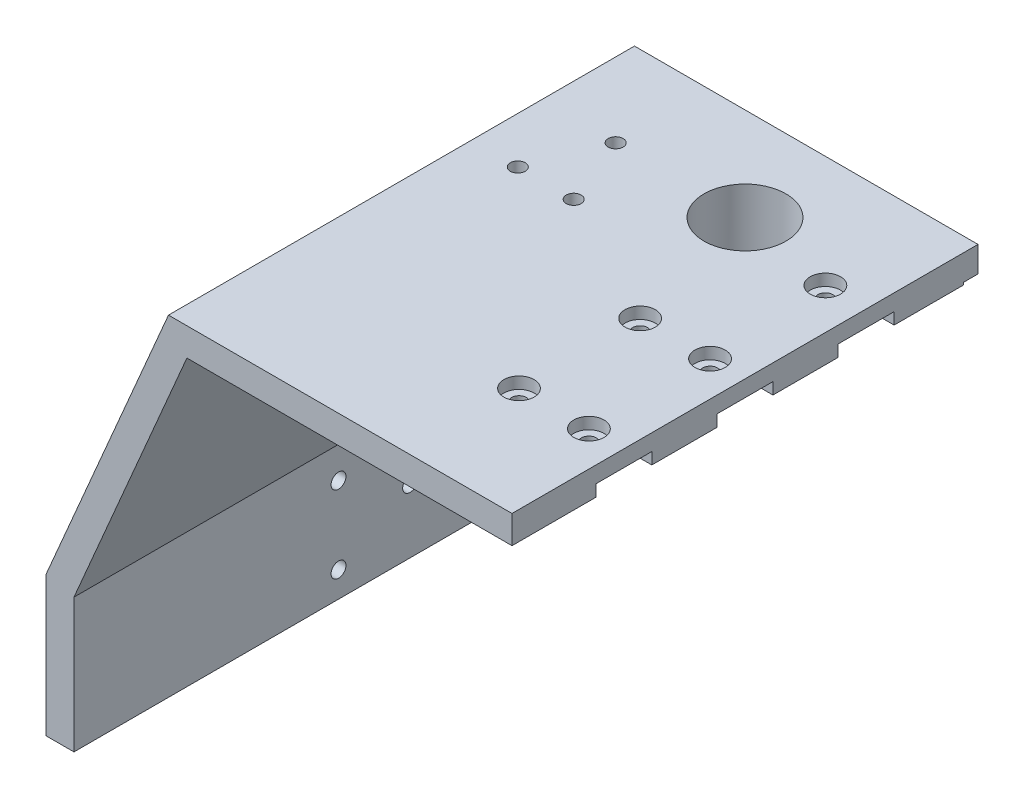
SolidWorks part; units mm, degrees
ref_plane "Alzado" through (0, 0, 0) normal (0, 0, 1) x (1, 0, 0)
ref_plane "Planta" through (0, 0, 0) normal (0, 1, 0) x (1, 0, 0)
ref_plane "Vista lateral" through (0, 0, 0) normal (1, 0, 0) x (0, 0, -1)
sketch "Croquis1" plane through (0, 0, 0) normal (0, 0, 1) x (1, 0, 0)
  line L1 (-100, 25) -> (-73.7179, 86.3249) construction
  line L2 (-73.7179, 86.3249) -> (73.7179, 86.3249) construction
  line L3 (100, 25) -> (100, -5) construction
  line L4 (100, 25) -> (73.7179, 86.3249) construction
  line L5 (-100, 25) -> (-100, -5)
  line L6 (-100, 25) -> (-73.7179, 86.3249)
  line L7 (-73.7179, 86.3249) -> (73.7179, 86.3249)
  line L8 (100, 25) -> (100, -5)
  line L9 (100, 25) -> (73.7179, 86.3249)
  line L10 (-94, 23.7685) -> (-94, -5)
  line L11 (-94, 23.7685) -> (-69.7615, 80.3249)
  line L12 (-69.7615, 80.3249) -> (69.7615, 80.3249)
  line L13 (94, 23.7685) -> (69.7615, 80.3249)
  line L14 (94, 23.7685) -> (94, -5)
  line L15 (-94, -5) -> (-100, -5)
  line L16 (100, -5) -> (94, -5)
  dimension "D2" = 30
  dimension "D1" = 6
extrude "Saliente-Extruir1" add sketch "Croquis1" along normal blind 100
sketch "Croquis3" plane through (0, 86.3249, 0) normal (0, 1, 0) x (1, 0, 0)
  line L0 (73.7179, 0) -> (-73.7179, 0) construction
  line L1 (73.7179, -100) -> (73.7179, 0) construction
  line L2 (-73.7179, -100) -> (-73.7179, 0) construction
  circle A2 centre (-30, -20) radius 8.8
  circle A3 centre (30, -20) radius 8.8
  dimension "D4" = 17.6
  dimension "D5" = 17.6
  dimension "D1" = 20
  dimension "D2" = 20
  dimension "D3" = 43.7179
  dimension "D6" = 43.7179
extrude "Cortar-Extruir1" cut sketch "Croquis3" against normal up to next
ref_plane "Plano1" through (-87.4795, 68.8361, 0) normal (-0.7859, 0.6184, 0) x (0, 0, -1)
sketch "Croquis4" plane through (-87.4795, 68.8361, 0) normal (-0.7859, 0.6184, 0) x (0, 0, -1)
  line L0 (0, -22.254) -> (0, 42.1921) construction
  line L1 (-100, -22.254) -> (0, -22.254) construction
  line L2 (-100, -22.254) -> (-100, 42.1921) construction
  line L3 (-100, 42.1921) -> (0, 42.1921) construction
  line L4 (0, -22.254) -> (0, 42.1921) construction
  line L5 (-100, -22.254) -> (0, -22.254) construction
  line L6 (-100, -22.254) -> (-100, 42.1921) construction
  line L7 (-100, 42.1921) -> (0, 42.1921) construction
  line L8 (0, 9.9691) -> (-100, 9.9691) construction
  circle A0 centre (-20, 9.9691) radius 8.8
  dimension "D1" = 17.6
  dimension "D2" = 20
extrude "Cortar-Extruir2" cut sketch "Croquis4" against normal up to next
mirror "Simetría1" about plane through (0, 0, 0) normal (1, 0, 0) of "Cortar-Extruir2"
sketch "Croquis5" plane through (0, 80.3249, 0) normal (0, -1, 0) x (1, 0, 0)
  line L0 (15.175, 0) -> (15.175, 2.3)
  line L1 (15.175, 2.3) -> (3.7842, 2.3)
  line L3 (-3.7842, 2.3) -> (-15.175, 2.3)
  line L4 (-15.175, 2.3) -> (-15.175, 0)
  line L10 (-14.875, 0) -> (-3.2619, 0)
  line L11 (3.2619, 0) -> (14.875, 0)
  line L12 (14.875, 0) -> (14.875, 2)
  line L13 (14.875, 2) -> (3.7202, 2)
  line L14 (-3.7202, 2) -> (-14.875, 2)
  line L15 (-14.875, 2) -> (-14.875, 0)
  line L17 (-15.175, 0) -> (3.2619, 0)
  line L19 (-3.2619, 0) -> (15.175, 0)
  line L20 (14.875, 0) -> (14.875, 2)
  line L22 (14.875, 2) -> (3.7202, 2)
  line L23 (-3.7202, 2) -> (-14.875, 2)
  line L24 (-14.875, 2) -> (-14.875, 0)
  arc A0 (3.7842, 2.3) -> (-3.7842, 2.3) centre (0, -6.25) ccw
  arc A3 (3.2619, 0) -> (-3.2619, 0) centre (0, -6.25) ccw
  arc A4 (3.7202, 2) -> (-3.7202, 2) centre (0, -6.25) ccw
  arc A5 (3.2619, 0) -> (-3.2619, 0) centre (0, -6.25) ccw
  arc A7 (3.7202, 2) -> (-3.7202, 2) centre (0, -6.25) ccw
  dimension "D1" = 0
  dimension "D2" = 0.3
extrude "Cortar-Extruir3" cut sketch "Croquis5" against normal blind 0.5
sketch "Croquis6" plane through (-100, 0, 0) normal (-1, 0, 0) x (0, 0, 1)
  circle A0 centre (43.227, 0.4977) radius 1.6 construction
  circle A1 centre (27.8635, 8.7685) radius 1.6 construction
  circle A2 centre (43.227, 17.0392) radius 1.6 construction
  circle A3 centre (43.227, 0.4977) radius 1.6
  circle A4 centre (27.8635, 8.7685) radius 1.6
  circle A5 centre (43.227, 17.0392) radius 1.6
extrude "Cortar-Extruir4" cut sketch "Croquis6" against normal up to next
sketch "Croquis7" plane through (-100, 0, 0) normal (-1, 0, 0) x (0, 0, 1)
  circle A0 centre (27.8635, 8.7685) radius 3.25
  circle A1 centre (43.227, 0.4977) radius 3.25
  circle A2 centre (43.227, 17.0392) radius 3.25
  dimension "D1" = 6.5
extrude "Cortar-Extruir5" cut sketch "Croquis7" against normal blind 2.5
mirror "Simetría2" about plane through (0, 0, 0) normal (1, 0, 0) of "Cortar-Extruir5", "Cortar-Extruir4"
sketch "Croquis8" plane through (0, 80.3249, 0) normal (0, -1, 0) x (1, 0, 0)
  line L0 (0, 100) -> (0, 0) construction
  line L1 (-37.5, 82) -> (37.5, 82)
  line L3 (-37.5, 70) -> (37.5, 70)
  line L5 (-69.7615, 100) -> (69.7615, 100) construction
  line L7 (-37.5, 56) -> (37.5, 56)
  line L8 (-37.5, 56) -> (-37.5, 44)
  line L9 (-37.5, 44) -> (37.5, 44)
  line L10 (37.5, 56) -> (37.5, 44)
  line L11 (-69.7615, 50) -> (69.7615, 50) construction
  line L12 (-69.7615, 100) -> (-69.7615, 0) construction
  line L13 (69.7615, 100) -> (69.7615, 0) construction
  line L14 (-17.5, 30) -> (17.5, 30)
  line L15 (-17.5, 30) -> (-17.5, 18)
  line L16 (-17.5, 18) -> (17.5, 18)
  line L17 (17.5, 30) -> (17.5, 18)
  line L19 (-73.7179, 0) -> (73.7179, 0) construction
  line L20 (-37.5, 76) -> (37.5, 76) construction
  line L21 (-37.5, 70) -> (-37.5, 82)
  line L24 (37.5, 82) -> (37.5, 70)
  point P29 (37.5, 76)
  dimension "D1" = 12
  dimension "D3" = 12
  dimension "D4" = 30
  dimension "D5" = 75
  dimension "D6" = 12
  dimension "D7" = 30
  dimension "D8" = 35
  dimension "D9" = 75
extrude "Cortar-Extruir6" cut sketch "Croquis8" against normal blind 2.5
sketch "Croquis9" plane through (0, 82.8249, 0) normal (0, -1, 0) x (1, 0, 0)
  line L0 (-37.4, 76) -> (37.4, 76) construction
  line L1 (-37.5, 50) -> (37.5, 50) construction
  line L2 (-37.5, 56) -> (-37.5, 44) construction
  line L3 (-37.4, 81.9) -> (-37.4, 70.1) construction
  line L4 (37.5, 44) -> (37.5, 56) construction
  line L5 (-17.5, 24) -> (17.5, 24) construction
  line L6 (37.4, 70.1) -> (37.4, 81.9) construction
  line L7 (-37.5, 82) -> (-37.5, 70) construction
  line L8 (73.7179, 0) -> (-73.7179, 0)
  line L9 (73.7179, -6) -> (73.7179, 0)
  line L10 (-73.7179, -6) -> (73.7179, -6)
  line L11 (-73.7179, 0) -> (-73.7179, -6)
  line L12 (73.7179, 0) -> (-73.7179, 0) construction
  line L14 (0, 100) -> (0, 0) construction
  line L15 (-69.7615, 100) -> (69.7615, 100) construction
  line L23 (-17.5, 30) -> (-17.5, 18) construction
  line L24 (17.5, 18) -> (17.5, 30) construction
  line L25 (-37.5, 56) -> (-37.5, 44) construction
  line L28 (0, 18) -> (-17.5, 30) construction
  line L29 (-17.5, 18) -> (17.5, 18) construction
  line L30 (0, 30) -> (-17.5, 18) construction
  line L31 (17.5, 30) -> (-17.5, 30) construction
  circle A7 centre (-22.5, 76) radius 1.6
  circle A8 centre (-7.5, 76) radius 1.6
  circle A9 centre (7.5, 76) radius 1.6
  circle A10 centre (22.5, 76) radius 1.6
  circle A15 centre (-22.5, 50) radius 1.6
  circle A16 centre (-7.5, 50) radius 1.6
  circle A17 centre (7.5, 50) radius 1.6
  circle A18 centre (22.5, 50) radius 1.6
  circle A19 centre (-8.75, 24) radius 1.6
  circle A21 centre (8.75, 24) radius 1.6
  dimension "D1" = 3.2
  dimension "D2" = 15
  dimension "D3" = 15
  dimension "D4" = 15
  dimension "D7" = 15
  dimension "D11" = 3.2
  dimension "D13" = 3.2
  dimension "D5" = 15
  dimension "D6" = 0
  dimension "D8" = 15
  dimension "D10" = 15
  dimension "D9" = 15
extrude "Cortar-Extruir7" cut sketch "Croquis9" against normal up to next
sketch "Croquis10" plane through (0, 86.3249, 0) normal (0, 1, 0) x (1, 0, 0)
  circle A0 centre (-22.5, -50) radius 3.25
  circle A1 centre (-7.5, -50) radius 3.25
  circle A2 centre (7.5, -50) radius 3.25
  circle A3 centre (22.5, -50) radius 3.25
  circle A4 centre (8.75, -24) radius 3.25
  circle A5 centre (-8.75, -24) radius 3.25
  circle A6 centre (22.5, -50) radius 1.6 construction
  circle A7 centre (7.5, -50) radius 1.6 construction
  circle A8 centre (-7.5, -50) radius 1.6 construction
  circle A9 centre (-22.5, -50) radius 1.6 construction
  circle A10 centre (22.5, -76) radius 3.25
  circle A11 centre (7.5, -76) radius 3.25
  circle A12 centre (-7.5, -76) radius 3.25
  circle A13 centre (-22.5, -76) radius 3.25
  circle A14 centre (-8.75, -24) radius 1.6 construction
  circle A15 centre (8.75, -24) radius 1.6 construction
  dimension "D1" = 6.5
  dimension "D2" = 6.5
  dimension "D3" = 6.5
  dimension "D4" = 6.5
  dimension "D5" = 6.5
extrude "Cortar-Extruir8" cut sketch "Croquis10" against normal blind 2.5
sketch "Croquis11" plane through (0, 80.3249, 0) normal (0, -1, 0) x (1, 0, 0)
  circle A0 centre (30, 20) radius 8.8 construction
  circle A1 centre (-30, 20) radius 8.8 construction
  circle A2 centre (30, 20) radius 8.8
  circle A3 centre (-30, 20) radius 8.8
  circle A4 centre (-30, 20) radius 10.3
  circle A5 centre (30, 20) radius 10.3
  dimension "D1" = 1.5
extrude "Saliente-Extruir2" add sketch "Croquis11" along normal blind 10
ref_plane "Plano2" through (-63.9034, 50.2844, 0) normal (-0.7859, 0.6184, 0) x (0, 0, -1)
sketch "Croquis12" plane through (-63.9034, 50.2844, 0) normal (-0.7859, 0.6184, 0) x (0, 0, -1)
  circle A0 centre (-20, 9.9691) radius 8.8 construction
  circle A1 centre (-20, 9.9691) radius 8.8
  circle A2 centre (-20, 9.9691) radius 10.3
  dimension "D1" = 1.5
extrude "Saliente-Extruir3" add sketch "Croquis12" along normal up to next
sketch "Croquis13" plane through (0, 80.3249, 0) normal (0, -1, 0) x (1, 0, 0)
  circle A0 centre (57.7615, 20) radius 1.6 construction
  circle A1 centre (51.7615, 35) radius 1.6 construction
  circle A2 centre (63.7615, 35) radius 1.6 construction
  circle A3 centre (-57.7615, 20) radius 1.6 construction
  circle A4 centre (-63.7615, 35) radius 1.6 construction
  circle A5 centre (-51.7615, 35) radius 1.6 construction
  circle A6 centre (57.7615, 20) radius 1.6
  circle A7 centre (51.7615, 35) radius 1.6
  circle A8 centre (63.7615, 35) radius 1.6
  circle A9 centre (-57.7615, 20) radius 1.6
  circle A10 centre (-63.7615, 35) radius 1.6
  circle A11 centre (-51.7615, 35) radius 1.6
extrude "Cortar-Extruir9" cut sketch "Croquis13" against normal up to next
sketch "Croquis14" plane through (0, 86.3249, 0) normal (0, 1, 0) x (1, 0, 0)
  line L1 (0, 0) -> (100, 0)
  line L2 (0, 0) -> (0, -100)
  line L3 (0, -100) -> (100, -100)
  line L4 (100, 0) -> (100, -100)
extrude "Cortar-Extruir10" cut sketch "Croquis14" against normal through all
